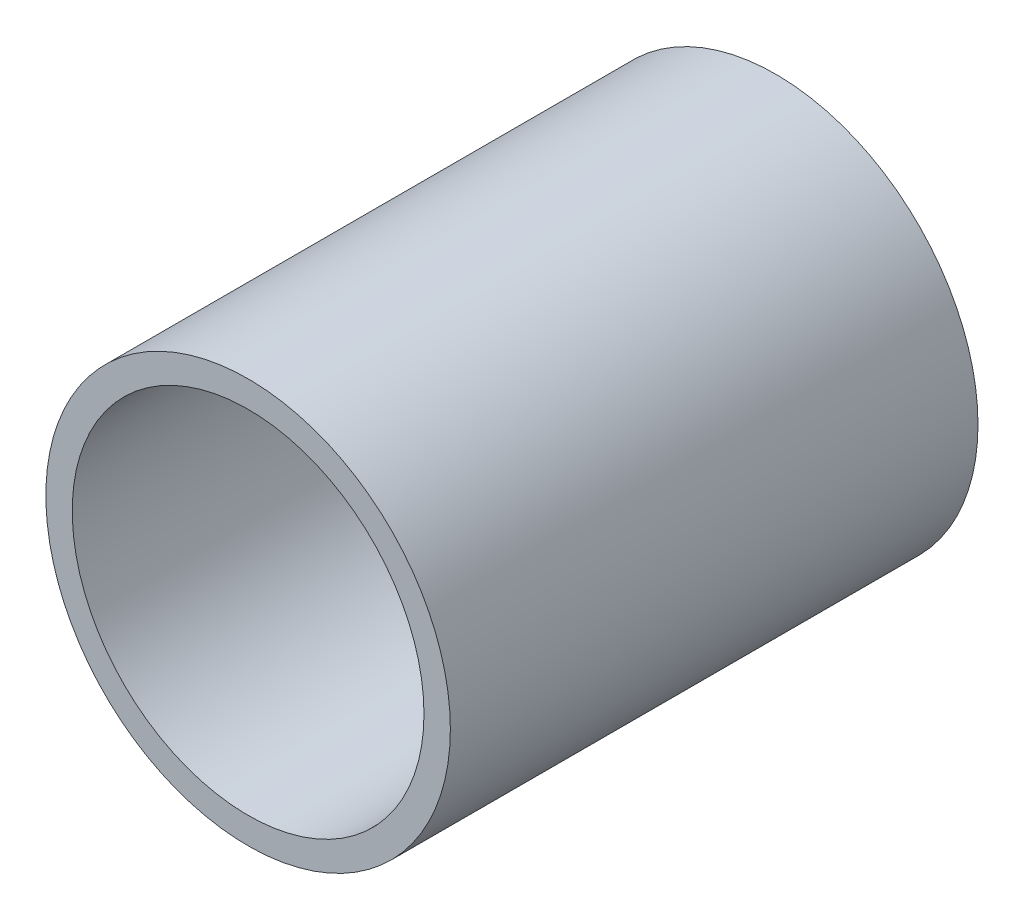
SolidWorks part; units mm, degrees
ref_plane "Alzado" through (0, 0, 0) normal (0, 0, 1) x (1, 0, 0)
ref_plane "Planta" through (0, 0, 0) normal (0, 1, 0) x (1, 0, 0)
ref_plane "Vista lateral" through (0, 0, 0) normal (1, 0, 0) x (0, 0, -1)
sketch "Croquis1" plane through (0, 0, 0) normal (0, 0, 1) x (1, 0, 0)
  circle A0 centre (0, 0) radius 10
  circle A1 centre (0, 0) radius 11.5
  dimension "D1" = 20
  dimension "D2" = 23
extrude "Saliente-Extruir1" add sketch "Croquis1" along normal mid plane 30
